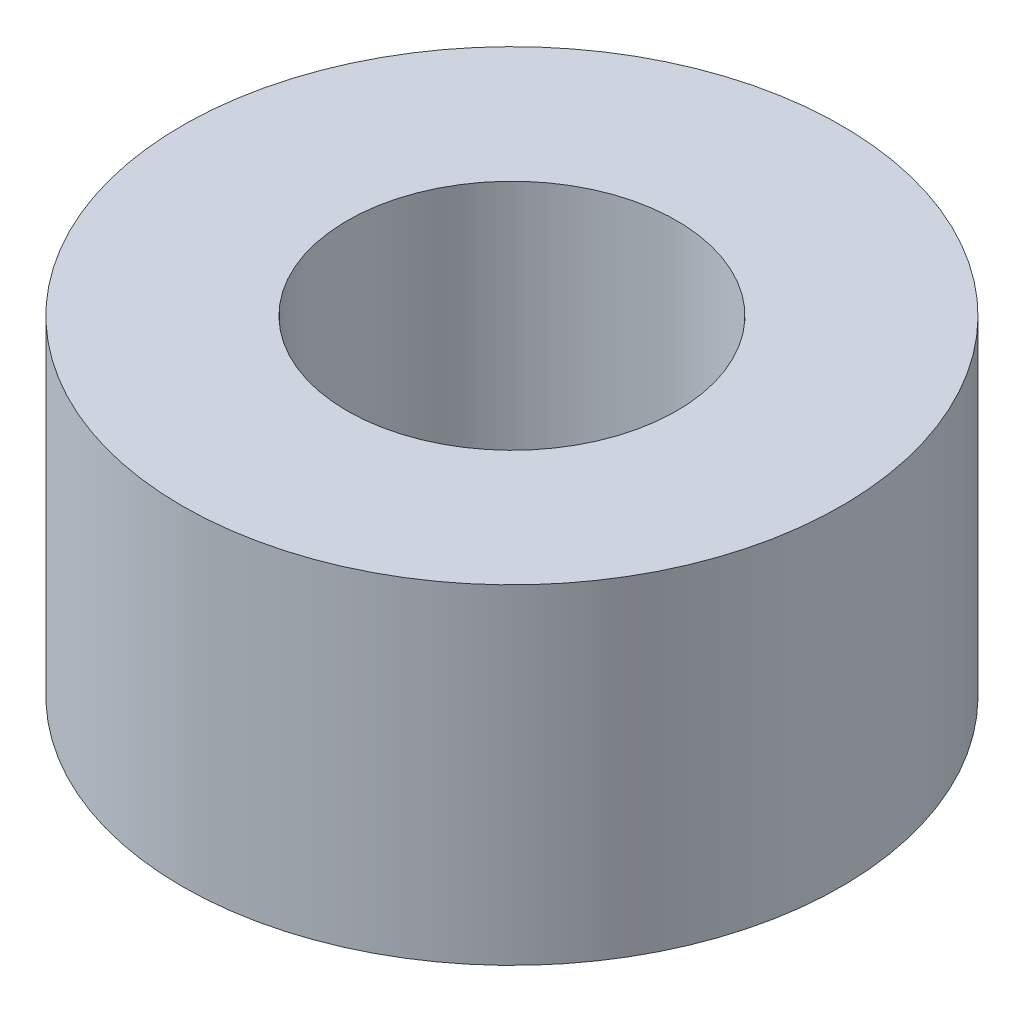
SolidWorks part; units mm, degrees
ref_plane "Front Plane" through (0, 0, 0) normal (0, 0, 1) x (1, 0, 0)
ref_plane "Top Plane" through (0, 0, 0) normal (0, 1, 0) x (1, 0, 0)
ref_plane "Right Plane" through (0, 0, 0) normal (1, 0, 0) x (0, 0, -1)
sketch "Sketch1" plane through (0, 0, 0) normal (0, 1, 0) x (1, 0, 0)
  circle A0 centre (0, 0) radius 2
  circle A1 centre (0, 0) radius 1
  dimension "D1" = 4
  dimension "D2" = 2
extrude "Boss-Extrude1" add sketch "Sketch1" along normal blind 2
